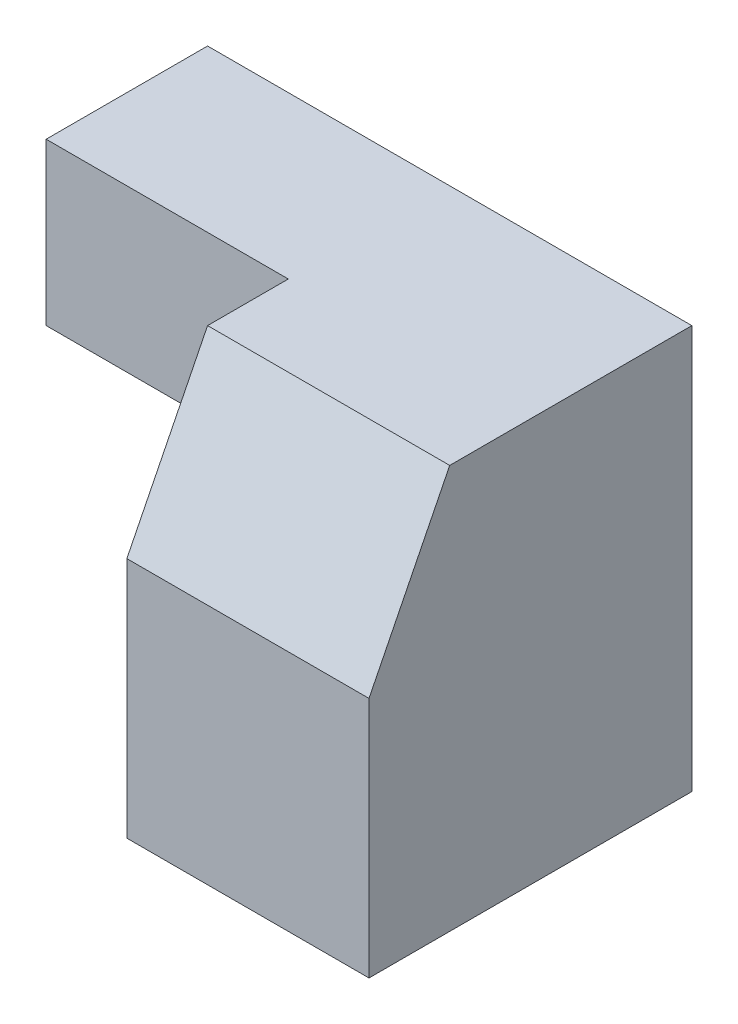
SolidWorks part; units mm, degrees
ref_plane "Front Plane" through (0, 0, 0) normal (0, 0, 1) x (1, 0, 0)
ref_plane "Top Plane" through (0, 0, 0) normal (0, 1, 0) x (1, 0, 0)
ref_plane "Right Plane" through (0, 0, 0) normal (1, 0, 0) x (0, 0, -1)
sketch "Sketch1" plane through (0, 0, 0) normal (0, 0, 1) x (1, 0, 0)
  line L1 (0, 0) -> (30, 0)
  line L2 (0, 0) -> (0, 25)
  line L3 (0, 25) -> (30, 25)
  line L4 (30, 0) -> (30, 25)
  dimension "D1" = 30
  dimension "D2" = 25
extrude "Boss-Extrude1" add sketch "Sketch1" along normal blind 20
sketch "Sketch2" plane through (0, 0, 20) normal (0, 0, 1) x (1, 0, 0)
  line L0 (30, 25) -> (0, 25) construction
  line L1 (0, 0) -> (15, 0)
  line L2 (0, 0) -> (0, 25)
  line L3 (0, 25) -> (15, 25)
  line L4 (15, 0) -> (15, 25)
extrude "Cut-Extrude1" cut sketch "Sketch2" against normal blind 10
sketch "Sketch3" plane through (15, 0, 0) normal (-1, 0, 0) x (0, 0, 1)
  line L0 (15, 25) -> (20, 15)
  line L1 (10, 25) -> (20, 25) construction
  line L2 (20, 0) -> (20, 25) construction
  line L3 (20, 15) -> (20, 25)
  line L4 (20, 25) -> (15, 25)
  dimension "D1" = 10
extrude "Cut-Extrude2" cut sketch "Sketch3" against normal blind 20
sketch "Sketch4" plane through (0, 0, 0) normal (-1, 0, 0) x (0, 0, 1)
  line L0 (10, 25) -> (10, 0) construction
  line L1 (0, 0) -> (10, 0)
  line L2 (0, 0) -> (0, 15)
  line L3 (0, 15) -> (10, 15)
  line L4 (10, 0) -> (10, 15)
  dimension "D1" = 15
extrude "Cut-Extrude3" cut sketch "Sketch4" against normal blind 15
